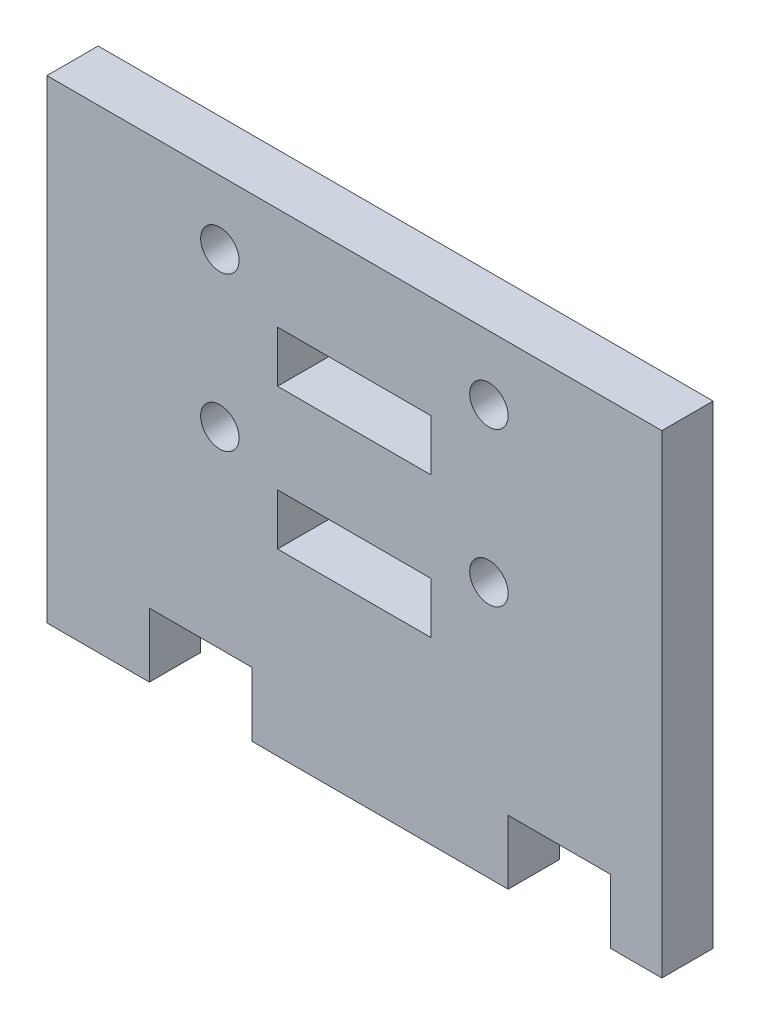
SolidWorks part; units mm, degrees
ref_plane "Front Plane" through (0, 0, 0) normal (0, 0, 1) x (1, 0, 0)
ref_plane "Top Plane" through (0, 0, 0) normal (0, 1, 0) x (1, 0, 0)
ref_plane "Right Plane" through (0, 0, 0) normal (1, 0, 0) x (0, 0, -1)
sketch "Sketch1" plane through (0, 0, 0) normal (0, 0, 1) x (1, 0, 0)
  line L0 (5, 2) -> (9, 2)
  line L1 (5, -0.5) -> (1, -0.5)
  line L2 (1, 18) -> (25, 18)
  line L3 (1, -0.5) -> (1, 18)
  line L4 (10, 14) -> (10, 12)
  line L5 (16, 14) -> (10, 14)
  line L6 (10, 12) -> (16, 12)
  line L7 (16, 12) -> (16, 14)
  line L8 (5, 2) -> (5, -0.5)
  line L9 (23, -0.5) -> (25, -0.5)
  line L10 (25, -0.5) -> (25, 18)
  line L11 (19, -0.5) -> (19, 2)
  line L12 (16, 6.5) -> (16, 8.5)
  line L13 (10, 6.5) -> (16, 6.5)
  line L14 (23, 2) -> (23, -0.5)
  line L15 (16, 8.5) -> (10, 8.5)
  line L16 (10, 8.5) -> (10, 6.5)
  line L17 (19, 2) -> (23, 2)
  line L18 (9, -0.5) -> (9, 2)
  line L19 (9, -0.5) -> (19, -0.5)
  circle A0 centre (7.75, 15.5) radius 0.75
  circle A1 centre (18.25, 15.5) radius 0.75
  circle A2 centre (18.25, 9.5) radius 0.75
  circle A3 centre (7.75, 9.5) radius 0.75
  dimension "D2" = 1
  dimension "D3" = 5
  dimension "D4" = 7.75
  dimension "D5" = 18.25
  dimension "D1" = 1.5
  dimension "D6" = 10
  dimension "D7" = 16
  dimension "D8" = 2
  dimension "D9" = 6.5
  dimension "D10" = 9.5
  dimension "D11" = 25
  dimension "D12" = 12
  dimension "D13" = 15.5
  dimension "D14" = 18
  dimension "D15" = 0.5
extrude "Boss-Extrude1" add sketch "Sketch1" along normal blind 2
